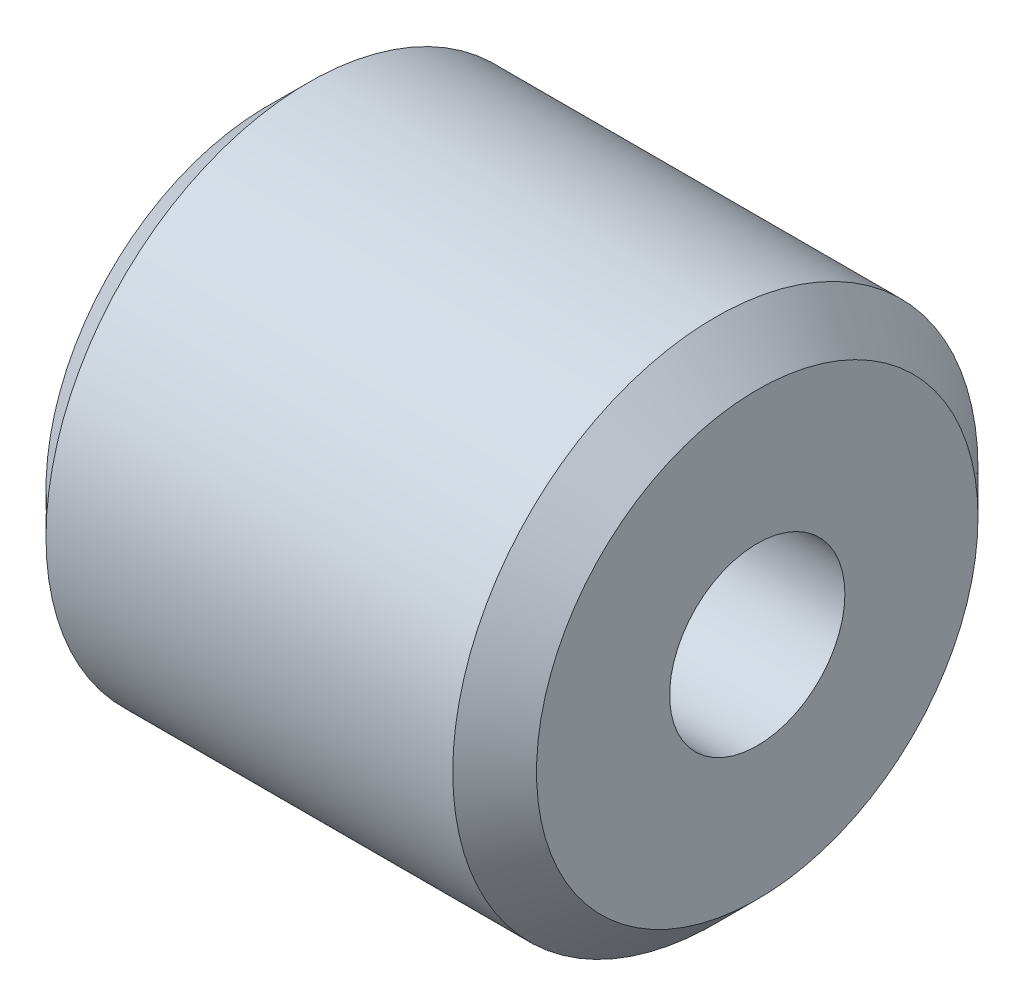
SolidWorks part; units mm, degrees
ref_plane "Alzado" through (0, 0, 0) normal (0, 0, 1) x (1, 0, 0)
ref_plane "Planta" through (0, 0, 0) normal (0, 1, 0) x (1, 0, 0)
ref_plane "Vista lateral" through (0, 0, 0) normal (1, 0, 0) x (0, 0, -1)
sketch "Croquis1" plane through (0, 0, 0) normal (1, 0, 0) x (0, 0, -1)
  circle A0 centre (0, 0) radius 1.59
  circle A1 centre (0, 0) radius 4.765
  dimension "D1" = 3.18
  dimension "D2" = 9.53
extrude "Saliente-Extruir1" add sketch "Croquis1" along normal mid plane 8.9
chamfer "Chaflán1" distance 0.76 angle 45 2 edges at (-4.45, 0, -4.765) (4.45, 0, -4.765)
